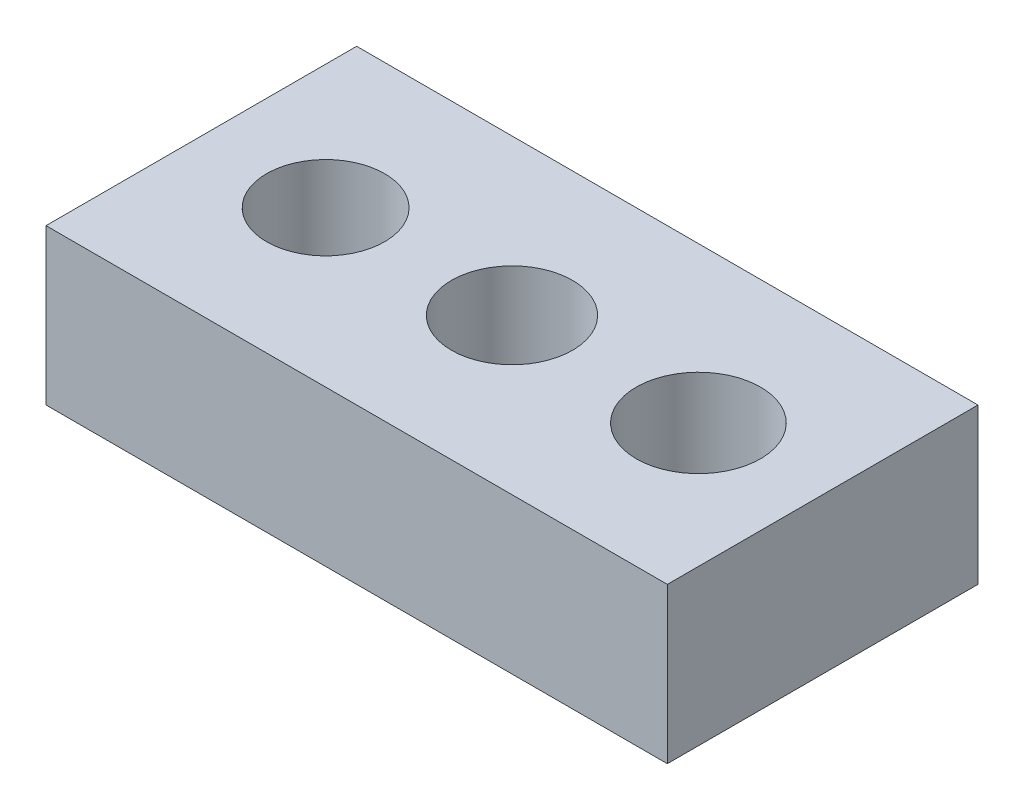
SolidWorks part; units mm, degrees
ref_plane "Front Plane" through (0, 0, 0) normal (0, 0, 1) x (1, 0, 0)
ref_plane "Top Plane" through (0, 0, 0) normal (0, 1, 0) x (1, 0, 0)
ref_plane "Right Plane" through (0, 0, 0) normal (1, 0, 0) x (0, 0, -1)
sketch "Sketch1" plane through (0, 0, 0) normal (0, 1, 0) x (1, 0, 0)
  line L1 (0, 0) -> (20, 0)
  line L2 (0, 0) -> (0, 10)
  line L3 (0, 10) -> (20, 10)
  line L4 (20, 0) -> (20, 10)
  dimension "D1" = 10
  dimension "D2" = 20
extrude "Boss-Extrude1" add sketch "Sketch1" along normal blind 5
sketch "Sketch2" plane through (0, 5, 0) normal (0, 1, 0) x (1, 0, 0)
  line L0 (0, 10) -> (0, 0) construction
  line L1 (0, 0) -> (20, 0) construction
  point P0 (4, 5)
  point P5 (10, 5)
  point P6 (16, 5)
  dimension "D1" = 4
  dimension "D2" = 5
  dimension "D3" = 3
hole_wizard "Tap Drill for M4x0.7 Tap1" positions "3DSketch1" profile "Sketch4" hole size "M4x0.7" standard "ANSI Metric" end condition through all
sketch3d "3DSketch1"
  point P0 (4, 5, -5)
sketch "Sketch4" plane through (4, 5, -5) normal (1, 0, 0) x (0, 0, 1)
  line L0 (0, 0) -> (0, 5)
  line L1 (0, 5) -> (1.9, 5)
  line L2 (1.9, 5) -> (1.9, 0)
  line L5 (1.9, 0) -> (0, 0)
  line L11 (0, -6.35) -> (0, 107.95) construction
  dimension "Thru Hole Dia." = 3.8
  dimension "Thru Hole Depth" = 5
hole_wizard "Tap Drill for M4x0.7 Tap2" positions "3DSketch2" profile "Sketch5" hole size "M4x0.7" standard "ANSI Metric" end condition through all
sketch3d "3DSketch2"
  point P0 (10, 5, -5)
sketch "Sketch5" plane through (10, 5, -5) normal (1, 0, 0) x (0, 0, 1)
  line L0 (0, 0) -> (0, 5)
  line L1 (0, 5) -> (1.95, 5)
  line L2 (1.95, 5) -> (1.95, 0)
  line L5 (1.95, 0) -> (0, 0)
  line L11 (0, -6.35) -> (0, 107.95) construction
  dimension "Thru Hole Dia." = 3.9
  dimension "Thru Hole Depth" = 5
hole_wizard "Tap Drill for M4x0.7 Tap3" positions "3DSketch3" profile "Sketch6" hole size "M4x0.7" standard "ANSI Metric" end condition through all
sketch3d "3DSketch3"
  point P0 (16, 5, -5)
sketch "Sketch6" plane through (16, 5, -5) normal (1, 0, 0) x (0, 0, 1)
  line L0 (0, 0) -> (0, 5)
  line L1 (0, 5) -> (2, 5)
  line L2 (2, 5) -> (2, 0)
  line L5 (2, 0) -> (0, 0)
  line L11 (0, -6.35) -> (0, 107.95) construction
  dimension "Thru Hole Dia." = 4
  dimension "Thru Hole Depth" = 5
